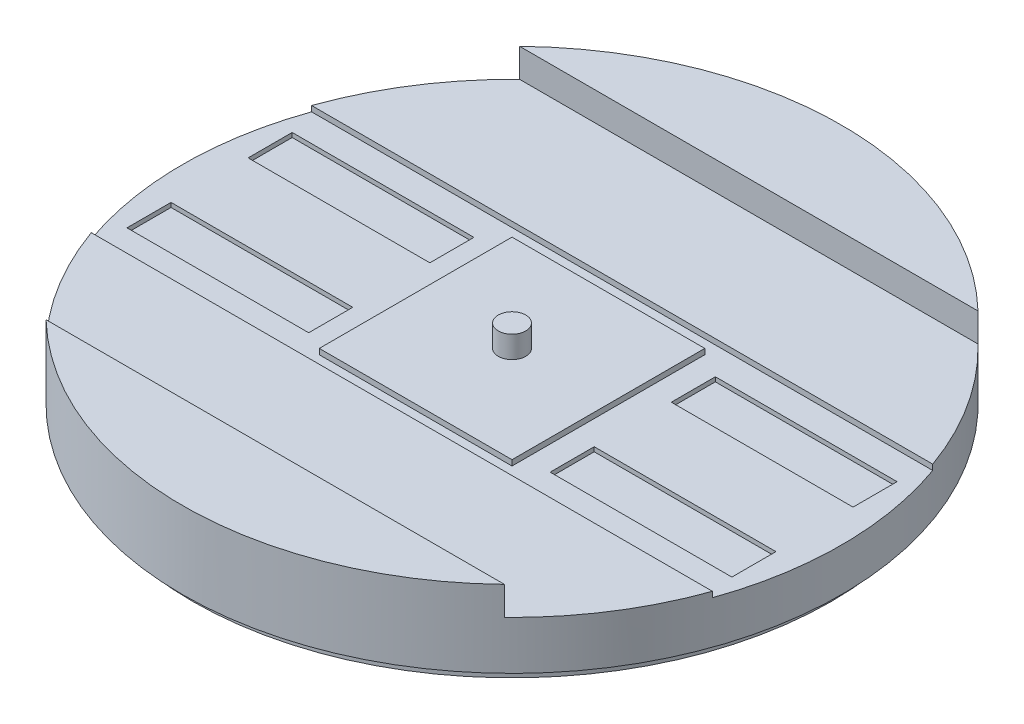
SolidWorks part; units mm, degrees
ref_plane "Front Plane" through (0, 0, 0) normal (0, 0, 1) x (1, 0, 0)
ref_plane "Top Plane" through (0, 0, 0) normal (0, 1, 0) x (1, 0, 0)
ref_plane "Right Plane" through (0, 0, 0) normal (1, 0, 0) x (0, 0, -1)
sketch "Sketch2" plane through (0, 0, 0) normal (0, 1, 0) x (1, 0, 0)
  circle A0 centre (0, 0) radius 76
  dimension "D1" = 152
extrude "Boss-Extrude1" add sketch "Sketch2" along normal blind 17.78
sketch "Sketch6" plane through (0, 17.78, 0) normal (0, 1, 0) x (1, 0, 0)
  line L0 (-76, 0) -> (76, 0) construction
  line L1 (-76, 54.61) -> (76, 54.61)
  line L2 (-76, -54.61) -> (76, -54.61)
  circle A0 centre (0, 0) radius 76 construction
  arc A1 (-76, 54.61) -> (-76, -54.61) centre (-76, 0) ccw
  arc A2 (76, -54.61) -> (76, 54.61) centre (76, 0) ccw
  point P6 (0, 0)
  dimension "D1" = 54.61
extrude "Cut-Extrude3" cut sketch "Sketch6" against normal blind 6.604
sketch "Sketch8" plane through (0, 11.176, 0) normal (0, 1, 0) x (1, 0, 0)
  line L0 (0, 76) -> (0, -76) construction
  line L1 (35.56, 76) -> (35.56, -76)
  line L2 (-35.56, 76) -> (-35.56, -76)
  arc A0 (-52.8559, -54.61) -> (52.8559, -54.61) centre (0, 0) ccw construction
  arc A1 (35.56, 76) -> (-35.56, 76) centre (0, 76) ccw
  arc A2 (-35.56, -76) -> (35.56, -76) centre (0, -76) ccw
  point P6 (0, 0)
  dimension "D1" = 35.56
extrude "Cut-Extrude4" [suppressed] cut sketch "Sketch8" along normal through all
sketch "Sketch9" plane through (0, 11.176, 0) normal (0, 1, 0) x (1, 0, 0)
  line L3 (-76, 0) -> (76, 0) construction
  line L4 (-76, 25.4) -> (-25.4, 25.4)
  line L5 (-76, -25.4) -> (-25.4, -25.4)
  line L8 (25.4, 25.4) -> (76, 25.4)
  line L9 (25.4, -25.4) -> (76, -25.4)
  line L10 (-25.4, 25.4) -> (25.4, 25.4)
  line L11 (-25.4, -25.4) -> (25.4, -25.4)
  arc A3 (52.8559, -54.61) -> (52.8559, 54.61) centre (0, 0) ccw construction
  arc A4 (-76, 25.4) -> (-76, -25.4) centre (-76, 0) ccw
  arc A5 (76, -25.4) -> (76, 25.4) centre (76, 0) ccw
  point P6 (0, 0)
  point P12 (0, 0)
  dimension "D2" = 25.4
extrude "Cut-Extrude5" cut sketch "Sketch9" against normal blind 1.27
sketch "Sketch10" plane through (0, 9.906, 0) normal (0, 1, 0) x (1, 0, 0)
  line L1 (-76, 0) -> (76, 0) construction
  line L20 (-69.7539, 19.05) -> (-27.8439, 19.05)
  line L21 (-69.7539, 19.05) -> (-69.7539, 8.89)
  line L22 (-69.7539, 8.89) -> (-27.8439, 8.89)
  line L23 (-27.8439, 19.05) -> (-27.8439, 8.89)
  line L24 (71.6299, 25.4) -> (-71.6299, 25.4) construction
  line L25 (-69.7539, -8.89) -> (-27.8439, -8.89)
  line L26 (-27.8439, -19.05) -> (-27.8439, -8.89)
  line L27 (-69.7539, -19.05) -> (-27.8439, -19.05)
  line L28 (-69.7539, -19.05) -> (-69.7539, -8.89)
  line L29 (69.7539, -19.05) -> (69.7539, -8.89)
  line L30 (69.7539, -19.05) -> (27.8439, -19.05)
  line L31 (27.8439, -19.05) -> (27.8439, -8.89)
  line L32 (69.7539, -8.89) -> (27.8439, -8.89)
  line L33 (69.7539, 8.89) -> (27.8439, 8.89)
  line L34 (27.8439, 19.05) -> (27.8439, 8.89)
  line L35 (69.7539, 19.05) -> (27.8439, 19.05)
  line L36 (69.7539, 19.05) -> (69.7539, 8.89)
  arc A2 (-71.6299, 25.4) -> (-71.6299, -25.4) centre (0, 0) ccw construction
  arc A3 (71.6299, -25.4) -> (71.6299, 25.4) centre (0, 0) ccw construction
  dimension "D3" = 10.16
  dimension "D4" = 41.91
  dimension "D5" = 6.35
extrude "Cut-Extrude6" cut sketch "Sketch10" against normal blind 1.016
sketch "Sketch11" plane through (0, 9.906, 0) normal (0, 1, 0) x (1, 0, 0)
  line L1 (-22.225, 22.225) -> (22.225, 22.225)
  line L2 (-22.225, 22.225) -> (-22.225, -22.225)
  line L3 (-22.225, -22.225) -> (22.225, -22.225)
  line L4 (22.225, 22.225) -> (22.225, -22.225)
  line L5 (-22.225, 22.225) -> (22.225, -22.225) construction
  line L6 (-22.225, -22.225) -> (22.225, 22.225) construction
  point P0 (0, 0)
  dimension "D1" = 44.45
  dimension "D2" = 44.45
extrude "Boss-Extrude2" add sketch "Sketch11" along normal blind 1.27
sketch "Sketch12" plane through (0, 11.176, 0) normal (0, 1, 0) x (1, 0, 0)
  line L1 (-0.6205, 6.3196) -> (-0.3133, 7.4241)
  line L2 (-0.3133, 7.4241) -> (0.3133, 7.4241)
  line L3 (0.6205, 6.3196) -> (0.3133, 7.4241)
  line L4 (2.0112, 6.0231) -> (1.9575, 7.1682)
  line L5 (1.3465, 7.3077) -> (1.9575, 7.1682)
  line L6 (0.8013, 6.2992) -> (1.3465, 7.3077)
  line L7 (3.301, 5.4245) -> (3.5035, 6.5529)
  line L8 (2.9389, 6.8248) -> (3.5035, 6.5529)
  line L9 (2.1829, 5.963) -> (2.9389, 6.8248)
  line L10 (4.4253, 4.554) -> (4.8738, 5.609)
  line L11 (4.3839, 5.9997) -> (4.8738, 5.609)
  line L12 (3.4551, 5.3278) -> (4.3839, 5.9997)
  line L13 (5.3278, 3.4551) -> (5.9997, 4.3839)
  line L14 (5.609, 4.8738) -> (5.9997, 4.3839)
  line L15 (4.554, 4.4253) -> (5.609, 4.8738)
  line L16 (5.963, 2.1829) -> (6.8248, 2.9389)
  line L17 (6.5529, 3.5035) -> (6.8248, 2.9389)
  line L18 (5.4245, 3.301) -> (6.5529, 3.5035)
  line L19 (6.2992, 0.8013) -> (7.3077, 1.3465)
  line L20 (7.1682, 1.9575) -> (7.3077, 1.3465)
  line L21 (6.0231, 2.0112) -> (7.1682, 1.9575)
  line L22 (6.3196, -0.6205) -> (7.4241, -0.3133)
  line L23 (7.4241, 0.3133) -> (7.4241, -0.3133)
  line L24 (6.3196, 0.6205) -> (7.4241, 0.3133)
  line L25 (6.0231, -2.0112) -> (7.1682, -1.9575)
  line L26 (7.3077, -1.3465) -> (7.1682, -1.9575)
  line L27 (6.2992, -0.8013) -> (7.3077, -1.3465)
  line L28 (5.4245, -3.301) -> (6.5529, -3.5035)
  line L29 (6.8248, -2.9389) -> (6.5529, -3.5035)
  line L30 (5.963, -2.1829) -> (6.8248, -2.9389)
  line L31 (4.554, -4.4253) -> (5.609, -4.8738)
  line L32 (5.9997, -4.3839) -> (5.609, -4.8738)
  line L33 (5.3278, -3.4551) -> (5.9997, -4.3839)
  line L34 (3.4551, -5.3278) -> (4.3839, -5.9997)
  line L35 (4.8738, -5.609) -> (4.3839, -5.9997)
  line L36 (4.4253, -4.554) -> (4.8738, -5.609)
  line L37 (2.1829, -5.963) -> (2.9389, -6.8248)
  line L38 (3.5035, -6.5529) -> (2.9389, -6.8248)
  line L39 (3.301, -5.4245) -> (3.5035, -6.5529)
  line L40 (0.8013, -6.2992) -> (1.3465, -7.3077)
  line L41 (1.9575, -7.1682) -> (1.3465, -7.3077)
  line L42 (2.0112, -6.0231) -> (1.9575, -7.1682)
  line L43 (-0.6205, -6.3196) -> (-0.3133, -7.4241)
  line L44 (0.3133, -7.4241) -> (-0.3133, -7.4241)
  line L45 (0.6205, -6.3196) -> (0.3133, -7.4241)
  line L46 (-2.0112, -6.0231) -> (-1.9575, -7.1682)
  line L47 (-1.3465, -7.3077) -> (-1.9575, -7.1682)
  line L48 (-0.8013, -6.2992) -> (-1.3465, -7.3077)
  line L49 (-3.301, -5.4245) -> (-3.5035, -6.5529)
  line L50 (-2.9389, -6.8248) -> (-3.5035, -6.5529)
  line L51 (-2.1829, -5.963) -> (-2.9389, -6.8248)
  line L52 (-4.4253, -4.554) -> (-4.8738, -5.609)
  line L53 (-4.3839, -5.9997) -> (-4.8738, -5.609)
  line L54 (-3.4551, -5.3278) -> (-4.3839, -5.9997)
  line L55 (-5.3278, -3.4551) -> (-5.9997, -4.3839)
  line L56 (-5.609, -4.8738) -> (-5.9997, -4.3839)
  line L57 (-4.554, -4.4253) -> (-5.609, -4.8738)
  line L58 (-5.963, -2.1829) -> (-6.8248, -2.9389)
  line L59 (-6.5529, -3.5035) -> (-6.8248, -2.9389)
  line L60 (-5.4245, -3.301) -> (-6.5529, -3.5035)
  line L61 (-6.2992, -0.8013) -> (-7.3077, -1.3465)
  line L62 (-7.1682, -1.9575) -> (-7.3077, -1.3465)
  line L63 (-6.0231, -2.0112) -> (-7.1682, -1.9575)
  line L64 (-6.3196, 0.6205) -> (-7.4241, 0.3133)
  line L65 (-7.4241, -0.3133) -> (-7.4241, 0.3133)
  line L66 (-6.3196, -0.6205) -> (-7.4241, -0.3133)
  line L67 (-6.0231, 2.0112) -> (-7.1682, 1.9575)
  line L68 (-7.3077, 1.3465) -> (-7.1682, 1.9575)
  line L69 (-6.2992, 0.8013) -> (-7.3077, 1.3465)
  line L70 (-5.4245, 3.301) -> (-6.5529, 3.5035)
  line L71 (-6.8248, 2.9389) -> (-6.5529, 3.5035)
  line L72 (-5.963, 2.1829) -> (-6.8248, 2.9389)
  line L73 (-4.554, 4.4253) -> (-5.609, 4.8738)
  line L74 (-5.9997, 4.3839) -> (-5.609, 4.8738)
  line L75 (-5.3278, 3.4551) -> (-5.9997, 4.3839)
  line L76 (-3.4551, 5.3278) -> (-4.3839, 5.9997)
  line L77 (-4.8738, 5.609) -> (-4.3839, 5.9997)
  line L78 (-4.4253, 4.554) -> (-4.8738, 5.609)
  line L79 (-2.1829, 5.963) -> (-2.9389, 6.8248)
  line L80 (-3.5035, 6.5529) -> (-2.9389, 6.8248)
  line L81 (-3.301, 5.4245) -> (-3.5035, 6.5529)
  line L82 (-0.8013, 6.2992) -> (-1.3465, 7.3077)
  line L83 (-1.9575, 7.1682) -> (-1.3465, 7.3077)
  line L84 (-2.0112, 6.0231) -> (-1.9575, 7.1682)
  arc A0 (-0.6205, 6.3196) -> (-0.8013, 6.2992) centre (0, 0) ccw
  arc A1 (-2.0112, 6.0231) -> (-2.1829, 5.963) centre (0, 0) ccw
  arc A2 (-3.301, 5.4245) -> (-3.4551, 5.3278) centre (0, 0) ccw
  arc A3 (-4.4253, 4.554) -> (-4.554, 4.4253) centre (0, 0) ccw
  arc A4 (-5.3278, 3.4551) -> (-5.4245, 3.301) centre (0, 0) ccw
  arc A5 (-5.963, 2.1829) -> (-6.0231, 2.0112) centre (0, 0) ccw
  arc A6 (-6.2992, 0.8013) -> (-6.3196, 0.6205) centre (0, 0) ccw
  arc A7 (-6.3196, -0.6205) -> (-6.2992, -0.8013) centre (0, 0) ccw
  arc A8 (-6.0231, -2.0112) -> (-5.963, -2.1829) centre (0, 0) ccw
  arc A9 (-5.4245, -3.301) -> (-5.3278, -3.4551) centre (0, 0) ccw
  arc A10 (-4.554, -4.4253) -> (-4.4253, -4.554) centre (0, 0) ccw
  arc A11 (-3.4551, -5.3278) -> (-3.301, -5.4245) centre (0, 0) ccw
  arc A12 (-2.1829, -5.963) -> (-2.0112, -6.0231) centre (0, 0) ccw
  arc A13 (-0.8013, -6.2992) -> (-0.6205, -6.3196) centre (0, 0) ccw
  arc A14 (0.6205, -6.3196) -> (0.8013, -6.2992) centre (0, 0) ccw
  arc A15 (2.0112, -6.0231) -> (2.1829, -5.963) centre (0, 0) ccw
  arc A16 (3.301, -5.4245) -> (3.4551, -5.3278) centre (0, 0) ccw
  arc A17 (4.4253, -4.554) -> (4.554, -4.4253) centre (0, 0) ccw
  arc A18 (5.3278, -3.4551) -> (5.4245, -3.301) centre (0, 0) ccw
  arc A19 (5.963, -2.1829) -> (6.0231, -2.0112) centre (0, 0) ccw
  arc A20 (6.2992, -0.8013) -> (6.3196, -0.6205) centre (0, 0) ccw
  arc A21 (6.3196, 0.6205) -> (6.2992, 0.8013) centre (0, 0) ccw
  arc A22 (6.0231, 2.0112) -> (5.963, 2.1829) centre (0, 0) ccw
  arc A23 (5.4245, 3.301) -> (5.3278, 3.4551) centre (0, 0) ccw
  arc A24 (4.554, 4.4253) -> (4.4253, 4.554) centre (0, 0) ccw
  arc A25 (3.4551, 5.3278) -> (3.301, 5.4245) centre (0, 0) ccw
  arc A26 (2.1829, 5.963) -> (2.0112, 6.0231) centre (0, 0) ccw
  arc A27 (0.8013, 6.2992) -> (0.6205, 6.3196) centre (0, 0) ccw
  point P6 (0, 6.35)
  point P118 (0, 0)
  dimension "D1" = 12.7
  dimension "D2" = 28
extrude "Boss-Extrude3" [suppressed] add sketch "Sketch12" along normal blind 25.4
sketch "Sketch13" [suppressed] plane through (0, 29.21, 0) normal (0, 1, 0) x (1, 0, 0)
  circle A0 centre (0, 0) radius 3.175
  dimension "D1" = 6.35
extrude "Cut-Extrude7" [suppressed] cut sketch "Sketch13" against normal blind 5.08
sketch "Sketch14" plane through (0, 11.176, 0) normal (0, 1, 0) x (1, 0, 0)
  circle A0 centre (0, 0) radius 3.175
  dimension "D1" = 6.35
extrude "Boss-Extrude4" add sketch "Sketch14" along normal blind 5.08
sketch "Sketch15" plane through (0, 0, 0) normal (0, -1, 0) x (1, 0, 0)
  circle A0 centre (0, 0) radius 73.66
  dimension "D1" = 147.32
extrude "Boss-Extrude5" add sketch "Sketch15" along normal blind 2.54
sketch "Sketch16" plane through (0, -2.54, 0) normal (0, -1, 0) x (1, 0, 0)
  line L0 (0, 64.77) -> (0, -64.77) construction
  circle A2 centre (0, 64.77) radius 3.175
  circle A3 centre (0, -64.77) radius 3.175
  dimension "D2" = 6.35
  dimension "D1" = 129.54
extrude "Cut-Extrude8" cut sketch "Sketch16" against normal blind 12.7
